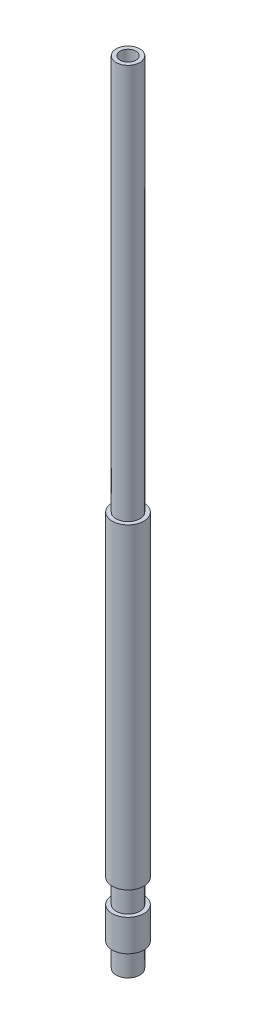
SolidWorks part; units mm, degrees
material "Простая углеродистая сталь"
ref_plane "Спереди" through (0, 0, 0) normal (0, 0, 1) x (1, 0, 0)
ref_plane "Сверху" through (0, 0, 0) normal (0, 1, 0) x (1, 0, 0)
ref_plane "Справа" through (0, 0, 0) normal (1, 0, 0) x (0, 0, -1)
sketch "Эскиз1" plane through (0, 0, 0) normal (0, 1, 0) x (1, 0, 0)
  circle A0 centre (0, 0) radius 1
  circle A1 centre (0, 0) radius 2
  dimension "D1" = 4
  dimension "D2" = 2
extrude "Бобышка-Вытянуть1" add sketch "Эскиз1" along normal blind 100
sketch "Эскиз2" plane through (0, 0, 0) normal (0, 0, 1) x (1, 0, 0)
  line L0 (2, 0) -> (1.5, 0)
  line L1 (2, 0) -> (2, 3)
  line L2 (1.5, 0) -> (1.5, 3)
  line L3 (2, 3) -> (1.5, 3)
  line L4 (0, 0) -> (0, 12.6474) construction
  line L5 (2, 7) -> (2, 10)
  line L6 (2, 7) -> (1.5, 7)
  line L7 (1.5, 7) -> (1.5, 10)
  line L10 (2, 10) -> (1.5, 10)
  dimension "D1" = 3
  dimension "D2" = 0.5
  dimension "D3" = 2
  dimension "D4" = 7
revolve "Вырез-Повернуть1" cut sketch "Эскиз2" angle 360 about L4
sketch "Эскиз3" plane through (0, 0, 0) normal (0, 0, 1) x (1, 0, 0)
  line L0 (0, 0) -> (0, 20) construction
  dimension "D1" = 20
sketch "Эскиз4" plane through (0, 0, 0) normal (0, 0, 1) x (1, 0, 0)
  line L0 (2, 100) -> (1.5, 100)
  line L1 (2, 100) -> (2, 50)
  line L2 (1.5, 100) -> (1.5, 50)
  line L3 (2, 50) -> (1.5, 50)
  dimension "D1" = 50
  dimension "D2" = 0.5
revolve "Вырез-Повернуть2" cut sketch "Эскиз4" angle 360 about L0
